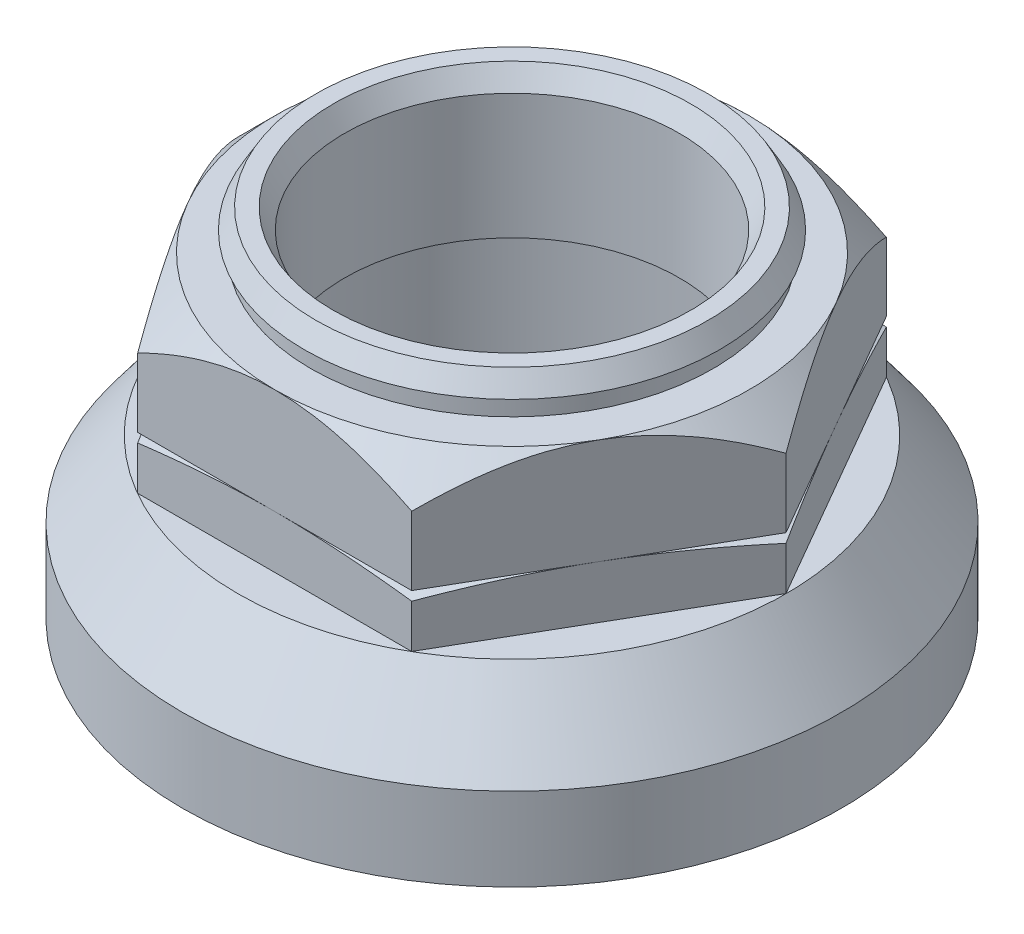
SolidWorks part; units mm, degrees
ref_plane "Front Plane" through (0, 0, 0) normal (0, 0, 1) x (1, 0, 0)
ref_plane "Top Plane" through (0, 0, 0) normal (0, 1, 0) x (1, 0, 0)
ref_plane "Right Plane" through (0, 0, 0) normal (1, 0, 0) x (0, 0, -1)
sketch "Sketch1" plane through (0, 0, 0) normal (1, 0, 0) x (0, 0, -1)
  line L0 (17, 2) -> (25, 2)
  line L2 (25, 2) -> (25, 8.3)
  line L3 (25, 8.3) -> (20.8, 14)
  line L4 (20.8, 14) -> (17, 14)
  line L5 (17, 14) -> (17, 2)
  line L6 (0, 2) -> (0, 14) construction
  dimension "D1" = 12
  dimension "D2" = 50
  dimension "D3" = 6.3
  dimension "D4" = 2
  dimension "D5" = 41.6
  dimension "D7" = 34
revolve "Revolve1" add sketch "Sketch1" angle 360 about L6
sketch "Sketch2" plane through (0, 14, 0) normal (0, 1, 0) x (1, 0, 0)
  line L1 (10.3923, 18) -> (-10.3923, 18)
  line L2 (-10.3923, 18) -> (-20.7846, 0)
  line L3 (-20.7846, 0) -> (-10.3923, -18)
  line L4 (-10.3923, -18) -> (10.3923, -18)
  line L5 (10.3923, -18) -> (20.7846, 0)
  line L6 (20.7846, 0) -> (10.3923, 18)
  circle A0 centre (0, 0) radius 18 construction
  circle A1 centre (0, 0) radius 17 construction
  circle A2 centre (0, 0) radius 17
  dimension "D1" = 36
extrude "Extrude1" add sketch "Sketch2" along normal blind 4
sketch "Sketch3" plane through (0, 0, 0) normal (1, 0, 0) x (0, 0, -1)
  line L0 (18, 18) -> (24, 16.5)
  line L1 (17, 18) -> (-17, 18) construction
  line L2 (0, 0) -> (0, 50) construction
  point P4 (17, 18)
  dimension "D1" = 1
  dimension "D2" = 6
  dimension "D3" = 1.5
  dimension "D4" = 50
surface "Surface-Revolve1" sketch "Sketch3" parameters "D1"=360
other "SurfaceCut1"
sketch "Sketch5" plane through (0, 18, 0) normal (0, 1, 0) x (1, 0, 0)
  line L1 (-20.7846, 0) -> (-10.3923, -18)
  line L2 (-10.3923, -18) -> (10.3923, -18)
  line L3 (10.3923, -18) -> (20.7846, 0)
  line L4 (20.7846, 0) -> (10.3923, 18)
  line L5 (10.3923, 18) -> (-10.3923, 18)
  line L6 (-10.3923, 18) -> (-20.7846, 0)
  circle A0 centre (0, 0) radius 18 construction
  circle A2 centre (0, 0) radius 12.7
  dimension "D2" = 25.4
  dimension "D1" = 36
extrude "Extrude2" add sketch "Sketch5" along normal blind 8 separate body
sketch "Sketch6" plane through (0, 0, 0) normal (1, 0, 0) x (0, 0, -1)
  line L0 (17, 16) -> (21, 16.5)
  line L1 (21, 16.5) -> (21, 23)
  line L2 (21, 23) -> (18, 26)
  line L3 (0, 0) -> (0, 100) construction
  dimension "D1" = 3
  dimension "D2" = 0.5
  dimension "D3" = 3
  dimension "D4" = 100
  dimension "D5" = 1
surface "Surface-Revolve2" sketch "Sketch6" parameters "D1"=360
other "SurfaceCut2"
sketch "Sketch7" plane through (0, 26, 0) normal (0, 1, 0) x (1, 0, 0)
  circle A0 centre (0, 0) radius 15.25
  circle A1 centre (0, 0) radius 12.7 construction
  circle A2 centre (0, 0) radius 12.7
  dimension "D1" = 30.5
extrude "Extrude3" add sketch "Sketch7" along normal blind 1.5
sketch "Sketch8" plane through (0, 27.5, 0) normal (0, 1, 0) x (1, 0, 0)
  circle A0 centre (0, 0) radius 12.7 construction
  circle A1 centre (0, 0) radius 12.7
  circle A2 centre (0, 0) radius 15.75
  dimension "D1" = 31.5
extrude "Extrude4" add sketch "Sketch8" along normal blind 1.5 draft 30
sketch "Sketch9" plane through (0, 0, 0) normal (1, 0, 0) x (0, 0, -1)
  line L0 (-25, 2) -> (25, 2) construction
  line L2 (19, 0) -> (17, 0)
  line L3 (0, 0) -> (0, -8) construction
  line L5 (17, 2) -> (22, 2)
  line L6 (17, 0) -> (17, 2)
  arc A0 (19, 0) -> (22, 2) centre (19, 3.25) ccw
  dimension "D1" = 8
  dimension "D2" = 38
  dimension "D3" = 44
revolve "Revolve2" add sketch "Sketch9" angle 360 about L3
